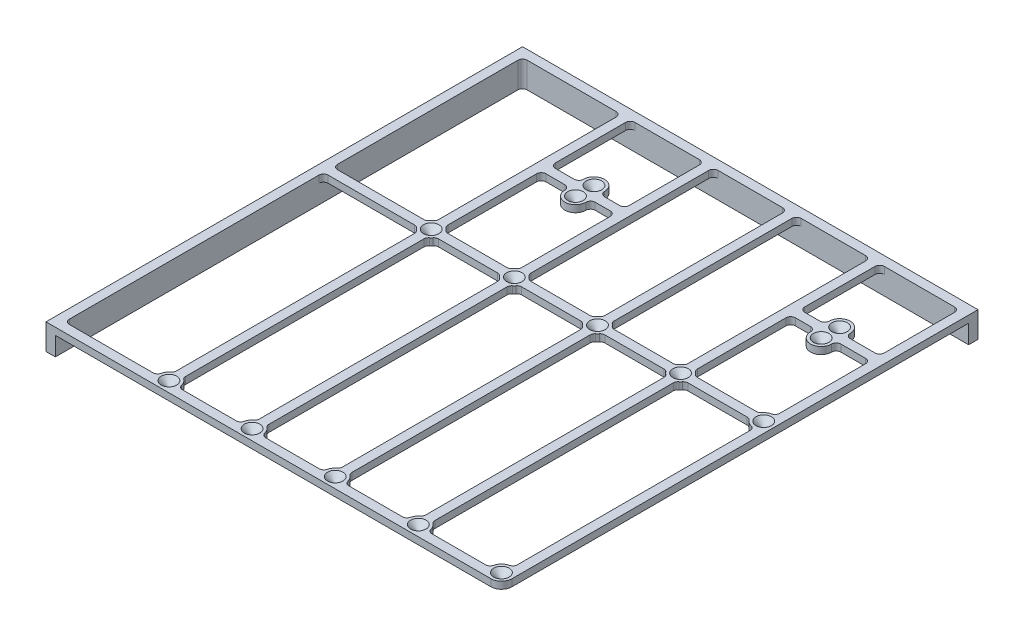
SolidWorks part; units mm, degrees
ref_plane "Front Plane" through (0, 0, 0) normal (0, 0, 1) x (1, 0, 0)
ref_plane "Top Plane" through (0, 0, 0) normal (0, 1, 0) x (1, 0, 0)
ref_plane "Right Plane" through (0, 0, 0) normal (1, 0, 0) x (0, 0, -1)
sketch "Sketch1" plane through (0, 0, 0) normal (0, 1, 0) x (1, 0, 0)
  line L0 (0, 0) -> (0, -199.5) construction
  line L1 (0, -199.5) -> (-4, -199.5)
  line L2 (-4, -199.5) -> (-4, 4)
  line L3 (-4, 4) -> (190.5, 4)
  line L4 (190.5, 4) -> (190.5, 0)
  line L5 (190.5, 0) -> (0, 0) construction
  line L6 (41.75, -80) -> (41.75, -83) construction
  line L7 (30, -80) -> (55.5, -80) construction
  line L8 (30, -80) -> (30, -198) construction
  line L9 (30, -198) -> (55.5, -198) construction
  line L10 (55.5, -80) -> (55.5, -198) construction
  line L11 (46.25, -80) -> (46.25, -83) construction
  line L12 (41.75, -198) -> (41.75, -195) construction
  line L13 (46.25, -198) -> (46.25, -195) construction
  line L14 (44, -195) -> (79.5, -195) construction
  line L15 (0, -199.5) -> (186, -199.5)
  line L16 (190.5, -195) -> (190.5, 0)
  line L17 (186.5, -190.5279) -> (186.5, -87.4721)
  line L18 (154.5311, -85) -> (181.9689, -85)
  line L19 (181.5279, -195.5) -> (154.9721, -195.5)
  line L20 (152.5, -190.9689) -> (152.5, -87.0311)
  line L21 (148.5, -190.9689) -> (148.5, -87.0311)
  line L22 (119.4721, -195.5) -> (146.0279, -195.5)
  line L23 (117, -190.9689) -> (117, -87.0311)
  line L24 (119.0311, -85) -> (146.4689, -85)
  line L25 (186.5, -139) -> (190.5, -139) construction
  line L26 (152.5, -139) -> (148.5, -139) construction
  line L27 (168.25, -195.5) -> (168.25, -199.5) construction
  line L28 (186.5, -190.5279) -> (186.0556, -194.5031) construction
  line L29 (83.5311, -85) -> (110.9689, -85)
  line L30 (48.0311, -85) -> (75.4689, -85)
  line L31 (48.4721, -195.5) -> (75.0279, -195.5)
  line L32 (83.9721, -195.5) -> (110.5279, -195.5)
  line L33 (39.5279, -195.5) -> (0, -195.5)
  line L34 (0, -195.5) -> (0, -85)
  line L35 (0, -85) -> (39.9689, -85)
  line L36 (42, -87.0311) -> (42, -190.9689)
  line L37 (46, -87.0311) -> (46, -190.9689)
  line L38 (77.5, -190.9689) -> (77.5, -87.0311)
  line L39 (81.5, -87.0311) -> (81.5, -190.9689)
  line L40 (113, -190.9689) -> (113, -87.0311)
  line L41 (115, -83) -> (115, -36) construction
  line L42 (62.545, -36) -> (167.455, -36) construction
  line L43 (167.455, -32.045) -> (167.455, -39.955) construction
  line L44 (62.545, -32.045) -> (62.545, -39.955) construction
  line L45 (58.045, -32.045) -> (58.045, -34)
  line L46 (171.05, -47) -> (58.95, -47) construction
  line L47 (171.05, -47) -> (171.05, -25) construction
  line L48 (171.05, -25) -> (58.95, -25) construction
  line L49 (58.95, -47) -> (58.95, -25) construction
  line L50 (171.05, -47) -> (58.95, -25) construction
  line L51 (171.05, -25) -> (58.95, -47) construction
  line L52 (67.045, -32.045) -> (67.045, -34)
  line L53 (39.9689, -81) -> (0, -81)
  line L54 (48.0311, -81) -> (75.4689, -81)
  line L55 (83.5311, -81) -> (110.9689, -81)
  line L56 (119.0311, -81) -> (146.4689, -81)
  line L57 (154.5311, -81) -> (181.9689, -81)
  line L58 (42, -78.9689) -> (42, 0)
  line L59 (42, 0) -> (0, 0)
  line L60 (0, 0) -> (0, -81)
  line L61 (46, -78.9689) -> (46, -38)
  line L62 (77.5, -78.9689) -> (77.5, -38)
  line L63 (81.5, -78.9689) -> (81.5, 0)
  line L64 (113, -78.9689) -> (113, 0)
  line L65 (117, -78.9689) -> (117, 0)
  line L66 (148.5, -78.9689) -> (148.5, 0)
  line L67 (152.5, -78.9689) -> (152.5, -38)
  line L68 (186.5, -78.5279) -> (186.5, -38)
  line L69 (186.5, 0) -> (152.5, 0)
  line L70 (148.5, 0) -> (117, 0)
  line L71 (113, 0) -> (81.5, 0)
  line L72 (77.5, 0) -> (46, 0)
  line L73 (168.25, -81) -> (168.25, -85) construction
  line L74 (46, -34) -> (58.045, -34)
  line L75 (46, -38) -> (58.045, -38)
  line L76 (67.045, -38) -> (77.5, -38)
  line L77 (67.045, -34) -> (77.5, -34)
  line L78 (162.955, -32.045) -> (162.955, -34)
  line L79 (171.955, -39.955) -> (171.955, -38)
  line L80 (171.955, -34) -> (186.5, -34)
  line L81 (162.955, -34) -> (152.5, -34)
  line L82 (162.955, -38) -> (152.5, -38)
  line L83 (171.955, -38) -> (186.5, -38)
  line L84 (171.955, -34) -> (171.955, -32.045)
  line L85 (162.955, -38) -> (162.955, -39.955)
  line L86 (152.5, -34) -> (152.5, 0)
  line L87 (186.5, -34) -> (186.5, 0)
  line L88 (77.5, -34) -> (77.5, 0)
  line L89 (58.045, -38) -> (58.045, -39.955)
  line L90 (46, -34) -> (46, 0)
  line L91 (67.045, -38) -> (67.045, -39.955)
  line L92 (52.0225, -34) -> (52.0225, -38) construction
  arc A0 (41.75, -195) -> (46.25, -195) centre (44, -195) cw construction
  arc A1 (41.75, -83) -> (46.25, -83) centre (44, -83) ccw construction
  circle A2 centre (44, -195) radius 0.5
  circle A3 centre (44, -83) radius 0.5
  circle A4 centre (79.5, -195) radius 0.5
  circle A5 centre (79.5, -83) radius 0.5
  circle A6 centre (115, -195) radius 0.5
  circle A7 centre (115, -83) radius 0.5
  circle A8 centre (150.5, -195) radius 0.5
  circle A9 centre (150.5, -83) radius 0.5
  circle A10 centre (186, -195) radius 0.5
  circle A11 centre (186, -83) radius 0.5
  arc A12 (186, -199.5) -> (190.5, -195) centre (186, -195) ccw
  arc A14 (181.5279, -195.5) -> (186.5, -190.5279) centre (186, -195) cw
  arc A15 (186.5, -87.4721) -> (181.9689, -85) centre (186, -83) cw
  arc A16 (154.5311, -85) -> (152.5, -87.0311) centre (150.5, -83) cw
  arc A17 (154.9721, -195.5) -> (152.5, -190.9689) centre (150.5, -195) ccw
  arc A18 (146.0279, -195.5) -> (148.5, -190.9689) centre (150.5, -195) cw
  arc A19 (119.4721, -195.5) -> (117, -190.9689) centre (115, -195) ccw
  arc A20 (110.5279, -195.5) -> (113, -190.9689) centre (115, -195) cw
  arc A21 (83.9721, -195.5) -> (81.5, -190.9689) centre (79.5, -195) ccw
  arc A22 (75.0279, -195.5) -> (77.5, -190.9689) centre (79.5, -195) cw
  arc A23 (48.4721, -195.5) -> (46, -190.9689) centre (44, -195) ccw
  arc A24 (39.5279, -195.5) -> (42, -190.9689) centre (44, -195) cw
  arc A25 (46, -87.0311) -> (48.0311, -85) centre (44, -83) ccw
  arc A26 (75.4689, -85) -> (77.5, -87.0311) centre (79.5, -83) ccw
  arc A27 (83.5311, -85) -> (81.5, -87.0311) centre (79.5, -83) cw
  arc A28 (110.9689, -85) -> (113, -87.0311) centre (115, -83) ccw
  arc A29 (119.0311, -85) -> (117, -87.0311) centre (115, -83) cw
  arc A30 (148.5, -87.0311) -> (146.4689, -85) centre (150.5, -83) cw
  arc A31 (42, -87.0311) -> (39.9689, -85) centre (44, -83) cw
  circle A32 centre (62.545, -32.045) radius 0.5
  circle A33 centre (62.545, -39.955) radius 0.5
  circle A34 centre (167.455, -32.045) radius 0.5
  circle A35 centre (167.455, -39.955) radius 0.5
  arc A37 (58.045, -39.955) -> (67.045, -39.955) centre (62.545, -39.955) ccw
  arc A38 (67.045, -32.045) -> (58.045, -32.045) centre (62.545, -32.045) ccw
  arc A39 (186.5, -78.5279) -> (181.9689, -81) centre (186, -83) ccw
  arc A40 (154.5311, -81) -> (152.5, -78.9689) centre (150.5, -83) ccw
  arc A41 (148.5, -78.9689) -> (146.4689, -81) centre (150.5, -83) ccw
  arc A42 (119.0311, -81) -> (117, -78.9689) centre (115, -83) ccw
  arc A43 (113, -78.9689) -> (110.9689, -81) centre (115, -83) ccw
  arc A44 (83.5311, -81) -> (81.5, -78.9689) centre (79.5, -83) ccw
  arc A45 (75.4689, -81) -> (77.5, -78.9689) centre (79.5, -83) cw
  arc A46 (48.0311, -81) -> (46, -78.9689) centre (44, -83) ccw
  arc A47 (39.9689, -81) -> (42, -78.9689) centre (44, -83) cw
  arc A48 (171.955, -32.045) -> (162.955, -32.045) centre (167.455, -32.045) ccw
  arc A49 (162.955, -39.955) -> (171.955, -39.955) centre (167.455, -39.955) ccw
  point P81 (118.9503, -192.8448)
  point P82 (47.182, -86.182)
  dimension "D4" = 112
  dimension "D9" = 1
  dimension "D12" = 4
  dimension "D13" = 4
  dimension "D14" = 7.91
  dimension "D2" = 25.5
  dimension "D3" = 118
  dimension "D5" = 4.5
  dimension "D6" = 14
  dimension "D7" = 30
  dimension "D8" = 80
  dimension "D10" = 5
  dimension "D11" = 35.5
  dimension "D15" = 104.91
  dimension "D16" = 22
  dimension "D17" = 112.1
  dimension "D18" = 25
  dimension "D19" = 203.5
  dimension "D20" = 194.5
extrude "Boss-Extrude1" add sketch "Sketch1" along normal blind 3
sketch "Sketch2" plane through (0, 0, 0) normal (0, -1, 0) x (1, 0, 0)
  line L1 (186.5, 0) -> (152.5, 0) construction
  line L2 (190.5, -4) -> (-4, -4) construction
  line L3 (-4, -4) -> (-4, 199.5) construction
  line L4 (-4, 199.5) -> (0, 199.5)
  line L6 (190.5, -4) -> (-4, -4)
  line L7 (-4, -4) -> (-4, 199.5)
  line L8 (-4, 199.5) -> (0, 199.5)
  line L9 (-4, 199.5) -> (186, 199.5) construction
  line L10 (0, 199.5) -> (0, 0)
  line L11 (0, 0) -> (190.5, 0)
  line L12 (190.5, 195) -> (190.5, -4) construction
  line L13 (190.5, 0) -> (190.5, -4)
extrude "Boss-Extrude2" add sketch "Sketch2" along normal blind 8 contours L13 L11 L10 L4 L7 L6
fillet "Fillet1" radius 2 83 edges at (152.5, 1.5, 190.9689) (154.9721, 1.5, 195.5) (119.4721, 1.5, 195.5) (117, 1.5, 190.9689) (81.5, 1.5, 190.9689) (83.9721, 1.5, 195.5) (46, 1.5, 190.9689) (48.4721, 1.5, 195.5) (81.5, 1.5, 87.0311) (81.5, 1.5, 0) (186.5, 1.5, 190.5279) (181.5279, 1.5, 195.5) (148.5, 1.5, 190.9689) (146.0279, 1.5, 195.5) (113, 1.5, 190.9689) (110.5279, 1.5, 195.5) (77.5, 1.5, 190.9689) (75.0279, 1.5, 195.5) (42, 1.5, 190.9689) (39.5279, 1.5, 195.5) (0, 1.5, 195.5) (0, -2.5, 0) (0, 1.5, 81) (0, 1.5, 85) (110.9689, 1.5, 85) (113, 1.5, 87.0311) (113, 1.5, 78.9689) (110.9689, 1.5, 81) (148.5, 1.5, 78.9689) (146.4689, 1.5, 81) (117, 1.5, 78.9689) (119.0311, 1.5, 81) (119.0311, 1.5, 85) (117, 1.5, 87.0311) (146.4689, 1.5, 85) (148.5, 1.5, 87.0311) (186.5, 1.5, 87.4721) (181.9689, 1.5, 85) (186.5, 1.5, 78.5279) (181.9689, 1.5, 81) (152.5, 1.5, 78.9689) (154.5311, 1.5, 81) (154.5311, 1.5, 85) (152.5, 1.5, 87.0311) (171.955, 1.5, 38) (152.5, 1.5, 38) (162.955, 1.5, 38) (186.5, 1.5, 38) (186.5, 1.5, 34) (162.955, 1.5, 34) (152.5, 1.5, 34) (171.955, 1.5, 34) (186.5, 1.5, 0) (148.5, 1.5, 0) (152.5, 1.5, 0) (117, 1.5, 0) (113, 1.5, 0) (42, 1.5, 0) (77.5, 1.5, 0) (46, 1.5, 0) (46, 1.5, 34) (77.5, 1.5, 34) (77.5, 1.5, 38) (58.045, 1.5, 34) (67.045, 1.5, 34) (67.045, 1.5, 38) (58.045, 1.5, 38) (46, 1.5, 38) (81.5, 1.5, 78.9689) (83.5311, 1.5, 81) (83.5311, 1.5, 85) (77.5, 1.5, 87.0311) (75.4689, 1.5, 85) (77.5, 1.5, 78.9689) (75.4689, 1.5, 81) (42, 1.5, 78.9689) (39.9689, 1.5, 81) (46, 1.5, 78.9689) (48.0311, 1.5, 81) (48.0311, 1.5, 85) (46, 1.5, 87.0311) (42, 1.5, 87.0311) (39.9689, 1.5, 85)
chamfer "Chamfer1" distance 2.8 angle 45 14 edges at (186, 3, 195.5) (150.5, 3, 195.5) (115, 3, 195.5) (79.5, 3, 195.5) (44, 3, 195.5) (44, 3, 83.5) (79.5, 3, 83.5) (115, 3, 83.5) (150.5, 3, 83.5) (186, 3, 83.5) (167.455, 3, 40.455) (167.455, 3, 32.545) (62.545, 3, 40.455) (62.545, 3, 32.545)
